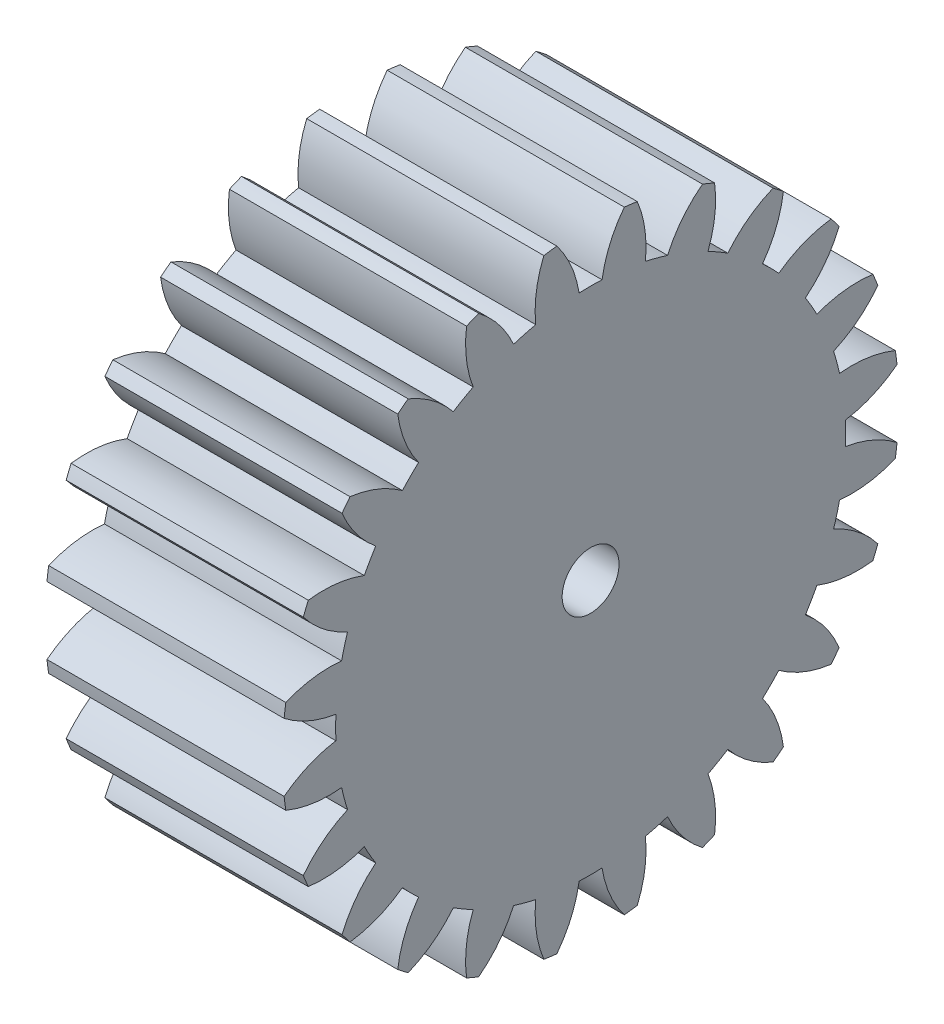
SolidWorks part; units mm, degrees
ref_plane "Plane1" through (0, 0, 0) normal (0, 0, 1) x (1, 0, 0)
ref_plane "Plane2" through (0, 0, 0) normal (0, 1, 0) x (1, 0, 0)
ref_plane "Plane3" through (0, 0, 0) normal (1, 0, 0) x (0, 0, -1)
other "Configuration Table"
sketch "HoldingSke" plane through (0, 0, 0) normal (0, 1, 0) x (1, 0, 0)
  line L0 (0, 0) -> (0.9135, -0.4067)
  line L1 (-15, 0) -> (100, 0) construction
  line L2 (0, 0) -> (-2.1039, 2.3779)
  line L3 (0, 0) -> (-11.863, 4.5341)
  line L4 (0, 0) -> (7.8894, 3.5126)
  line L5 (0, 0) -> (-46.8476, -17.4728)
  line L6 (0, 0) -> (-8.2896, -5.593)
  line L7 (-2.1039, 2.3779) -> (8.6586, 51.2059)
  line L8 (-76.2, 54.61) -> (-75.5, 54.61)
  line L9 (-71.009, 38.7566) -> (-53.1078, 45.2721)
  line L10 (-76.2, 71.12) -> (104.1128, 71.12)
  line L11 (0, 0) -> (-10, 0)
  line L12 (-76.2, 101.6) -> (-76.162, 101.6)
  line L13 (24.9733, 27.94) -> (52.9518, 28.4284)
  line L14 (24.9733, 27.94) -> (24.9743, 27.94)
  line L15 (24.9733, 27.94) -> (100.4006, 29.5858)
  line L16 (-63.627, -1) -> (-12.827, -1)
  circle A0 centre (0, 0) radius 1.2
  circle A1 centre (0, 0) radius 10.749
  circle A2 centre (0, 0) radius 37.5
  circle A3 centre (0, 0) radius 1.2
  dimension "MHD" = 21.498
  dimension "Hub_dia" = 75
  dimension "Bore" = 2.4
  dimension "MBD" = 2.4
  dimension "Num_teeth" = 24
  dimension "Pitch" = 1
  dimension "Overall_len" = 50
  dimension "Show_teeth" = 24
  dimension "Thickness" = 10
  dimension "OAL" = 50.0001
  dimension "T_dim" = 0.7
  dimension "Ap" = 20
  dimension "H" = 19.05
  dimension "Pitch_radius" = 180.3128
  dimension "Width" = 10
  dimension "Backlash" = 0.038
  dimension "Addendum_fac" = 1
  dimension "Dedendum_fac" = 1.25
  dimension "Clearance_fac" = 0.25
  dimension "Dedendum_add" = 0.001
  dimension "Module" = 1
sketch "BasProSke" plane through (0, 0, 0) normal (0, 1, 0) x (1, 0, 0)
  line L0 (-10, 0) -> (60, 0) construction
  line L1 (0, 0) -> (0, 13)
  line L2 (0, 0) -> (10, 0)
  line L3 (10, 0) -> (10, 13)
  line L4 (10, 13) -> (0, 13)
  dimension "Thickness" = 10
  dimension "Diameter" = 26
revolve "Base-Revolve" add sketch "BasProSke" angle 360 about L0
sketch "TooCutSke" plane through (0, 0, 0) normal (1, 0, 0) x (0, 0, -1)
  line L1 (0, 0) -> (0, 107) construction
  line L2 (0, 0) -> (-0.8513, 11.9698) construction
  line L3 (0, 0) -> (-3.127, 23.752) construction
  line L4 (-0.8513, 11.9698) -> (-1.5635, 11.876) construction
  arc A0 (0.4834, 10.7381) -> (-0.4834, 10.7381) centre (0, 0) ccw
  arc A1 (1.4409, 12.9455) -> (-1.4409, 12.9455) centre (0, 0) ccw
  circle A2 centre (0, 0) radius 12 construction
  circle A3 centre (0, 0) radius 11.2763 construction
  arc A4 (-0.4834, 10.7381) -> (-1.4409, 12.9455) centre (-5.2252, 9.9926) ccw
  arc A5 (1.4409, 12.9455) -> (0.4834, 10.7381) centre (5.2252, 9.9926) ccw
  dimension "Root_dia" = 21.498
  dimension "Overcut_dia" = 26.0508
  dimension "Pitch_dia" = 24
  dimension "Base_dia" = 22.5526
  dimension "Flank_rad" = 4.8
  dimension "Half_ang" = 7.5
  dimension "Half_CT" = 0.7183
extrude "ToothCut" cut sketch "TooCutSke" along normal through all
fillet "Breaks" [suppressed] radius 0.02
fillet "RootFillets" [suppressed] radius 0.251
pattern_circular "TeethCuts" count 24 every 15 about axis through (-10, 0, 0) along (1, 0, 0) of "ToothCut", "RootFillets", "Breaks"
sketch "HubNeaOneSke" plane through (0, 0, 0) normal (-1, 0, 0) x (0, 0, 1)
  circle A0 centre (0, 0) radius 10.749
  dimension "Diameter" = 21.498
extrude "HubNearOne" [suppressed] add sketch "HubNeaOneSke" along normal blind 40.0001
sketch "HubNeaBotSke" plane through (0, 0, 0) normal (-1, 0, 0) x (0, 0, 1)
  circle A0 centre (0, 0) radius 10.749
  dimension "Diameter" = 21.498
extrude "HubNearBoth" [suppressed] add sketch "HubNeaBotSke" along normal blind 20
ref_plane "FarPln" through (10, 0, 0) normal (1, 0, 0) x (0, 0, -1)
sketch "HubFarSke" plane through (10, 0, 0) normal (1, 0, 0) x (0, 0, -1)
  circle A0 centre (0, 0) radius 10.749
  dimension "Diameter" = 21.498
extrude "HubFar" [suppressed] add sketch "HubFarSke" along normal blind 20
sketch "BorSke" plane through (0, 0, 0) normal (1, 0, 0) x (0, 0, -1)
  circle A0 centre (0, 0) radius 1.2
  dimension "Diameter" = 2.4
extrude "Bore" cut sketch "BorSke" along normal mid plane 100.0001
sketch "KeySke" plane through (0, 0, 0) normal (1, 0, 0) x (0, 0, -1)
  line L0 (-0.8, 0) -> (-0.8, 1.9)
  line L1 (-0.8, 1.9) -> (0.8, 1.9)
  line L2 (0.8, 1.9) -> (0.8, 0)
  line L3 (0, 0) -> (0, 34) construction
  line L4 (-0.8, 0) -> (0.8, 0)
  dimension "Offset" = 1.9
  dimension "Width" = 1.6
extrude "Keyway" [suppressed] cut sketch "KeySke" along normal mid plane 100.0001
pattern_circular "Keyway2" [suppressed] count 2 every 90 about axis through (-10, 0, 0) along (1, 0, 0)
equation "' \"Module@HoldingSke\" = 6.35"
equation "' \"Num_teeth@HoldingSke\" = 12"
equation "' \"Ap@HoldingSke\" =  20"
equation "' \"Ap@HoldingSke\" = 20"
equation "' \"Width@HoldingSke\" = 0.5 * 25.4"
equation "' \"Hub_dia@HoldingSke\"= 1 * 25.4"
equation "' \"Hub_dia@HoldingSke\" = 1 * 25.4"
equation "' \"Overall_len@HoldingSke\" = 1.0 * 25.4"
equation "' \"Bore@HoldingSke\" = 0.75 * 25.4"
equation "' \"T_dim@HoldingSke\" = 0.1 * 25.4"
equation "' \"Width@KeySke\" = 0.25 * 25.4"
equation "' \"Show_teeth@HoldingSke\" = 13"
equation "' \"Backlash@HoldingSke\" = 0.009 * 25.4"
equation "' \"Addendum_fac@HoldingSke\" = 1.0"
equation "' \"Dedendum_fac@HoldingSke\" = 1.25"
equation "' \"Dedendum_add@HoldingSke\" = 0.00005 * 25.4"
equation "' \"Clearance_fac@HoldingSke\" = 0.25"
equation "\"Pitch@HoldingSke\" = 1 / \"Module@HoldingSke\""
equation "\"Overcut_dia@TooCutSke\" = (\"Num_teeth@HoldingSke\" + 2 * \"Addendum_fac@HoldingSke\") / \"Pitch@HoldingSke\" + 0.002 * 25.4"
equation "\"Pitch_dia@TooCutSke\" = \"Num_teeth@HoldingSke\" / \"Pitch@HoldingSke\""
equation "\"Base_dia@TooCutSke\" = \"Num_teeth@HoldingSke\" / \"Pitch@HoldingSke\" * cos((\"Ap@HoldingSke\"  * 3.14159265 / 180))"
equation "\"Root_dia@TooCutSke\" = (\"Num_teeth@HoldingSke\" + 2) / \"Pitch@HoldingSke\" - 2 * (\"Addendum_fac@HoldingSke\" + \"Dedendum_fac@HoldingSke\") / \"Pitch@HoldingSke\" - \"Dedendum_add@HoldingSke\" * 2"
equation "\"Half_ang@TooCutSke\" = 180 / \"Num_teeth@HoldingSke\""
equation "\"Half_CT@TooCutSke\" = \"Num_teeth@HoldingSke\" / \"Pitch@HoldingSke\" * sin((3.14159265 / 2 / \"Num_teeth@HoldingSke\")) / 2 - 7 * \"Backlash@HoldingSke\" / 4"
equation "\"Flank_rad@TooCutSke\" = \"Num_teeth@HoldingSke\" / \"Pitch@HoldingSke\" / 5"
equation "\"Radius@RootFillets\" = \"Clearance_fac@HoldingSke\" / \"Pitch@HoldingSke\" + \"Dedendum_add@HoldingSke\""
equation "\"Break_rad@Breaks\" = 0.02 / \"Pitch@HoldingSke\""
equation "\"Thickness@HoldingSke\" = \"Width@HoldingSke\""
equation "\"OAL@HoldingSke\" = \"Thickness@HoldingSke\""
equation "\"MHD@HoldingSke\" = (\"Num_teeth@HoldingSke\" + 2) / \"Pitch@HoldingSke\" - 2 * (\"Addendum_fac@HoldingSke\" + \"Dedendum_fac@HoldingSke\")  / \"Pitch@HoldingSke\" - \"Dedendum_add@HoldingSke\" * 2"
equation "\"MBD@HoldingSke\" = (\"Num_teeth@HoldingSke\" + 2) / \"Pitch@HoldingSke\" - 2 * (\"Addendum_fac@HoldingSke\" + \"Dedendum_fac@HoldingSke\")  / \"Pitch@HoldingSke\" - \"Dedendum_add@HoldingSke\" * 2 - 0.002 * 25.4"
equation "\"MHD@HoldingSke\" = ((sgn( \"MHD@HoldingSke\" - \"Hub_dia@HoldingSke\" )-1)*( \"MHD@HoldingSke\" - \"Hub_dia@HoldingSke\" ))/-2+ \"Hub_dia@HoldingSke\""
equation "\"MBD@HoldingSke\" = ((sgn( \"MBD@HoldingSke\" - \"Bore@HoldingSke\" )-1)*( \"MBD@HoldingSke\" - \"Bore@HoldingSke\" ))/-2+ \"Bore@HoldingSke\""
equation "\"OAL@HoldingSke\" = ((sgn( \"OAL@HoldingSke\" - \"Overall_len@HoldingSke\" )+1)*( \"OAL@HoldingSke\" - \"Overall_len@HoldingSke\" ))/2 + \"Overall_len@HoldingSke\" + 0.000002 * 25.4"
equation "\"Num_teeth@TeethCuts\" = int( \"Show_teeth@HoldingSke\" ) + 1"
equation "\"Num_teeth@TeethCuts\" = ((sgn( \"Num_teeth@TeethCuts\" - \"Num_teeth@HoldingSke\" )-1)*( \"Num_teeth@TeethCuts\" - \"Num_teeth@HoldingSke\" ))/-2+ \"Num_teeth@HoldingSke\""
equation "\"Num_teeth@TeethCuts\" = ((sgn( \"Num_teeth@TeethCuts\" - 2.0)+1)*( \"Num_teeth@TeethCuts\" - 2.0))/2 +2.0"
equation "\"Angle@TeethCuts\" = 360.0 / \"Num_teeth@HoldingSke\""
equation "\"Diameter@BasProSke\" = (\"Num_teeth@HoldingSke\" + 2 * \"Addendum_fac@HoldingSke\") / \"Pitch@HoldingSke\""
equation "\"Thickness@BasProSke\"  = \"Thickness@HoldingSke\""
equation "' \"Fillet_rad@BasProSke\" =  \"Thickness@HoldingSke\" * 0.05"
equation "' \"Fillet_rad@BasProSke\" = \"Thickness@HoldingSke\" * 0.05"
equation "\"MHD@HoldingSke\" = ((sgn( \"MHD@HoldingSke\" - \"Root_dia@TooCutSke\" )-1)*( \"MHD@HoldingSke\" - \"Root_dia@TooCutSke\" ))/-2+ \"Root_dia@TooCutSke\""
equation "\"Diameter@HubNeaOneSke\" = \"MHD@HoldingSke\""
equation "\"Length@HubNearOne\" = \"OAL@HoldingSke\" - \"Thickness@BasProSke\""
equation "\"Diameter@HubNeaBotSke\" = \"MHD@HoldingSke\""
equation "\"Length@HubNearBoth\" = ( \"OAL@HoldingSke\" - \"Thickness@BasProSke\" ) / 2.0"
equation "\"Thickness@FarPln\" = \"Thickness@BasProSke\""
equation "\"Diameter@HubFarSke\" = \"MHD@HoldingSke\""
equation "\"Length@HubFar\" = ( \"OAL@HoldingSke\" - \"Thickness@BasProSke\" ) / 2.0"
equation "\"Diameter@BorSke\" = \"MBD@HoldingSke\""
equation "\"D1@Bore\" = \"OAL@HoldingSke\" * 2.0"
equation "\"D1@Keyway\" = \"OAL@HoldingSke\" * 2.0"
equation "\"Offset@KeySke\" = \"T_dim@HoldingSke\" + \"MBD@HoldingSke\" / 2.0"
